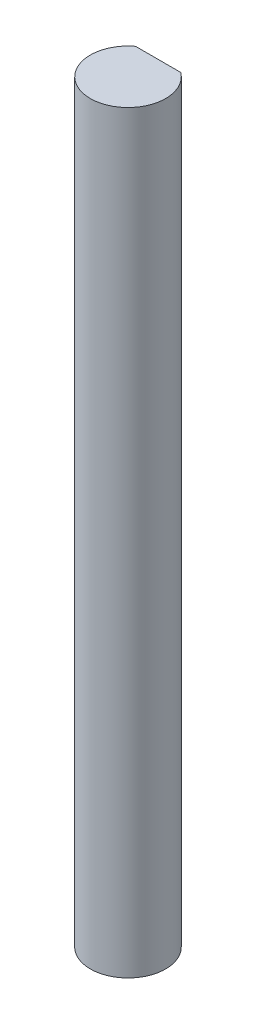
SolidWorks part; units mm, degrees
ref_plane "Front Plane" through (0, 0, 0) normal (0, 0, 1) x (1, 0, 0)
ref_plane "Top Plane" through (0, 0, 0) normal (0, 1, 0) x (1, 0, 0)
ref_plane "Right Plane" through (0, 0, 0) normal (1, 0, 0) x (0, 0, -1)
sketch "Sketch1" plane through (0, 0, 0) normal (0, 1, 0) x (1, 0, 0)
  line L0 (-1.905, 2.54) -> (1.905, 2.54)
  arc A0 (-1.905, 2.54) -> (1.905, 2.54) centre (0, 0) ccw
  dimension "D1" = 6.35
  dimension "D2" = 2.54
extrude "Boss-Extrude1" add sketch "Sketch1" along normal blind 63.5
